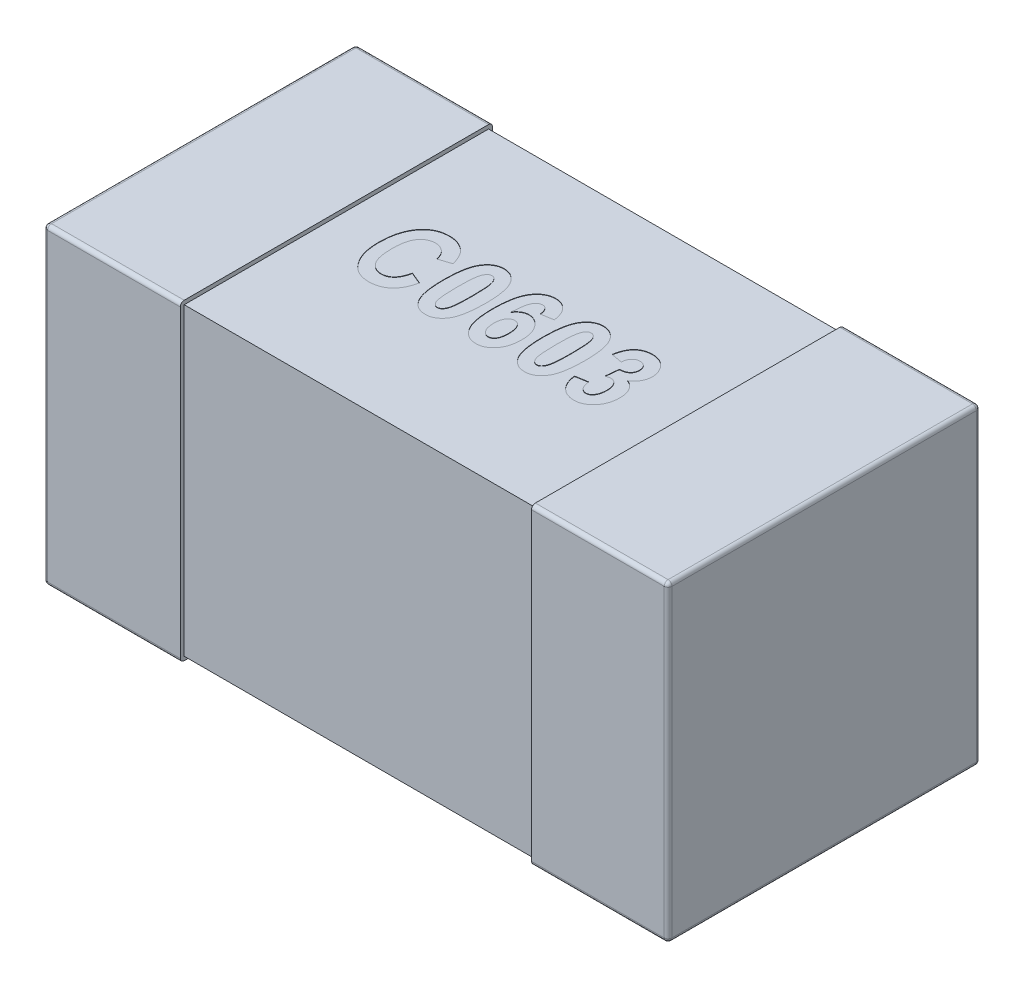
SolidWorks part; units mm, degrees
ref_plane "Front Plane" through (0, 0, 0) normal (0, 0, 1) x (1, 0, 0)
ref_plane "Top Plane" through (0, 0, 0) normal (0, 1, 0) x (1, 0, 0)
ref_plane "Right Plane" through (0, 0, 0) normal (1, 0, 0) x (0, 0, -1)
sketch "Sketch1" plane through (0, 0, 0) normal (0, 1, 0) x (1, 0, 0)
  line L0 (0, 0.15) -> (0, -0.15) construction
  line L1 (-0.8, 0) -> (0, 0) construction
  line L3 (-0.8, 0.4) -> (-0.45, 0.4)
  line L4 (-0.8, 0.4) -> (-0.8, -0.4)
  line L5 (-0.8, -0.4) -> (-0.45, -0.4)
  line L6 (-0.45, 0.4) -> (-0.45, -0.4)
  dimension "BANDWIDTH" = 0.35
  dimension "WIDTH" = 0.8
  dimension "LENGTH-HALF" = 0.8
extrude "THICKNESS" add sketch "Sketch1" along normal blind 0.8
fillet "Fillet1" radius 0.01 8 edges at (-0.8, 0, 0) (-0.625, 0, -0.4) (-0.8, 0.4, -0.4) (-0.625, 0, 0.4) (-0.8, 0.4, 0.4) (-0.8, 0.8, 0) (-0.625, 0.8, -0.4) (-0.625, 0.8, 0.4)
sketch "Sketch2" plane through (0, 0, 0) normal (1, 0, 0) x (0, 0, -1)
  line L0 (0, 0.8) -> (0, 0) construction
  line L1 (-0.39, 0.79) -> (0.39, 0.79)
  line L2 (-0.39, 0.79) -> (-0.39, 0.01)
  line L3 (-0.39, 0.01) -> (0.39, 0.01)
  line L4 (0.39, 0.79) -> (0.39, 0.01)
  line L5 (-0.39, 0.8) -> (0.39, 0.8) construction
  line L6 (-0.39, 0) -> (0.39, 0) construction
  line L7 (-0.4, 0.4) -> (0.4, 0.4) construction
  line L8 (-0.4, 0.79) -> (-0.4, 0.01) construction
  line L9 (0.4, 0.79) -> (0.4, 0.01) construction
  dimension "D1" = 0.01
  dimension "D2" = 0.01
extrude "Boss-Extrude2" add sketch "Sketch2" against normal up to surface (0.45 mm away) up to face at (-0.45, 0.4, 0)
mirror "Mirror3" about plane through (0, 0, 0) normal (1, 0, 0) of "Boss-Extrude2", "Fillet1", "THICKNESS"
sketch "Sketch3" plane through (0, 0.79, 0) normal (0, 1, 0) x (1, 0, 0)
  line L0 (-0.35, -0.1) -> (0.35, -0.1) construction
  line L1 (0, -0.44) -> (0, 0.44) construction
  line L2 (-0.44, 0) -> (0.44, 0) construction
  text T0 "<b>C0603</b>" font "Arial Narrow" height 0.2
  point P2 (0, -0.1)
  dimension "D1" = 0.7
  dimension "D2" = 0.1
extrude "Cut-Extrude1" cut sketch "Sketch3" against normal blind 0.001
